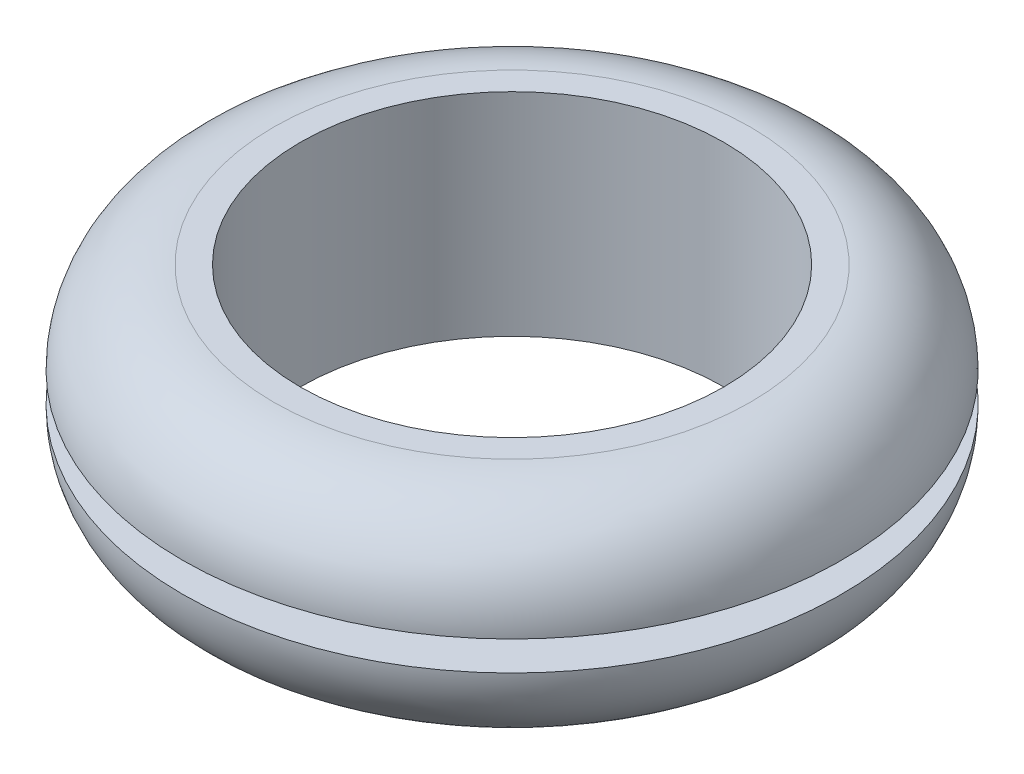
SolidWorks part; units mm, degrees
material "BUTYL"
ref_plane "Front Plane" through (0, 0, 0) normal (0, 0, 1) x (1, 0, 0)
ref_plane "Top Plane" through (0, 0, 0) normal (0, 1, 0) x (1, 0, 0)
ref_plane "Right Plane" through (0, 0, 0) normal (1, 0, 0) x (0, 0, -1)
sketch "Sketch2" plane through (0, 0, 0) normal (0, 1, 0) x (1, 0, 0)
  circle A0 centre (0, 0) radius 9
  circle A1 centre (0, 0) radius 14
  dimension "D1" = 18
  dimension "D2" = 28
extrude "Boss-Extrude1" add sketch "Sketch2" along normal blind 9
fillet "Fillet1" radius 3.875 2 edges at (0, 0, 14) (0, 9, 14)
sketch "Sketch3" plane through (0, 9, 0) normal (0, 1, 0) x (1, 0, 0)
  circle A0 centre (0, 0) radius 11
  circle A1 centre (0, 0) radius 15.875
  dimension "D1" = 22
  dimension "D2" = 31.75
extrude "Cut-Extrude1" cut sketch "Sketch3" against normal blind 1.25 from offset 3.875 offset against normal yes
